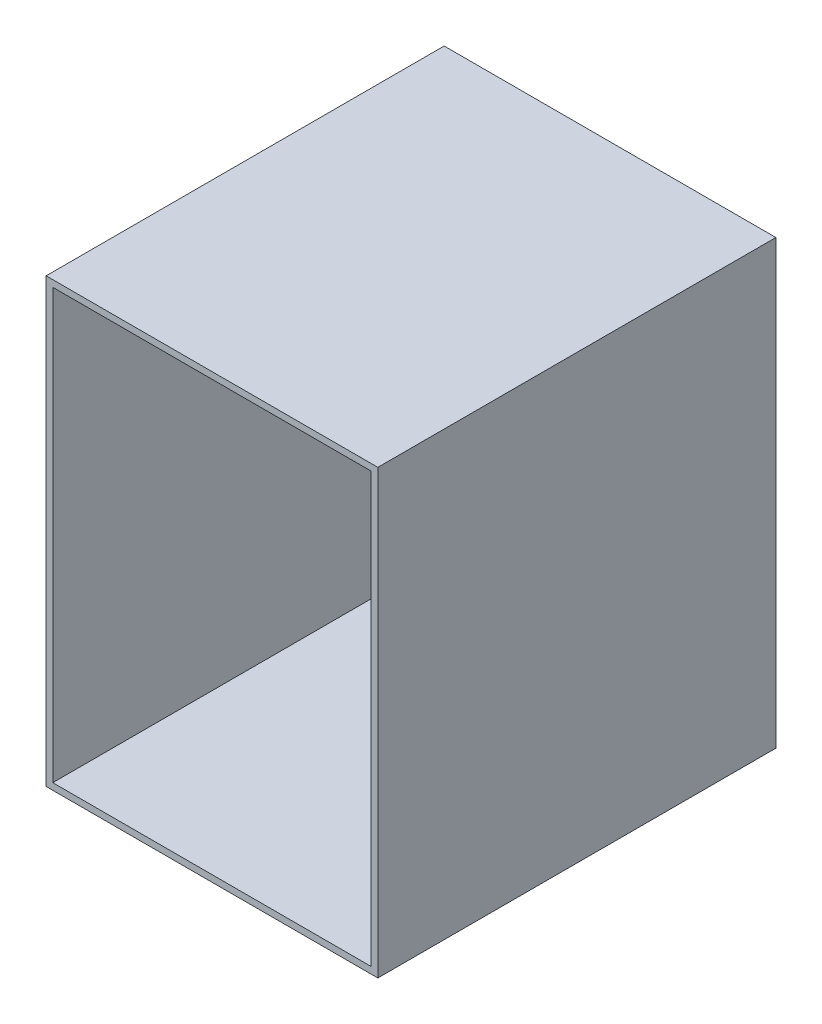
SolidWorks part; units mm, degrees
ref_plane "Piano frontale" through (0, 0, 0) normal (0, 0, 1) x (1, 0, 0)
ref_plane "Piano superiore" through (0, 0, 0) normal (0, 1, 0) x (1, 0, 0)
ref_plane "Piano destro" through (0, 0, 0) normal (1, 0, 0) x (0, 0, -1)
sketch "Schizzo1" plane through (0, 0, 0) normal (0, 0, 1) x (1, 0, 0)
  line L1 (-75, 100) -> (75, 100)
  line L2 (-75, 100) -> (-75, -100)
  line L3 (-75, -100) -> (75, -100)
  line L4 (75, 100) -> (75, -100)
  line L5 (-75, 100) -> (75, -100) construction
  line L6 (-75, -100) -> (75, 100) construction
  point P0 (0, 0)
  dimension "D1" = 200
  dimension "D2" = 150
extrude "Estrusione-Estrusione1" add sketch "Schizzo1" along normal blind 180 contours L1 L4 L3 L2
sketch "Schizzo2" plane through (0, 0, 180) normal (0, 0, 1) x (1, 0, 0)
  line L1 (-72, 97) -> (72, 97)
  line L2 (-72, 97) -> (-72, -97)
  line L3 (-72, -97) -> (72, -97)
  line L4 (72, 97) -> (72, -97)
  line L5 (-72, 97) -> (72, -97) construction
  line L6 (-72, -97) -> (72, 97) construction
  point P0 (0, 0)
  dimension "D1" = 194
  dimension "D2" = 144
extrude "Taglio-Estrusione1" cut sketch "Schizzo2" against normal offset from surface (175 mm away) 5 up to face at (0, 0, 0)
